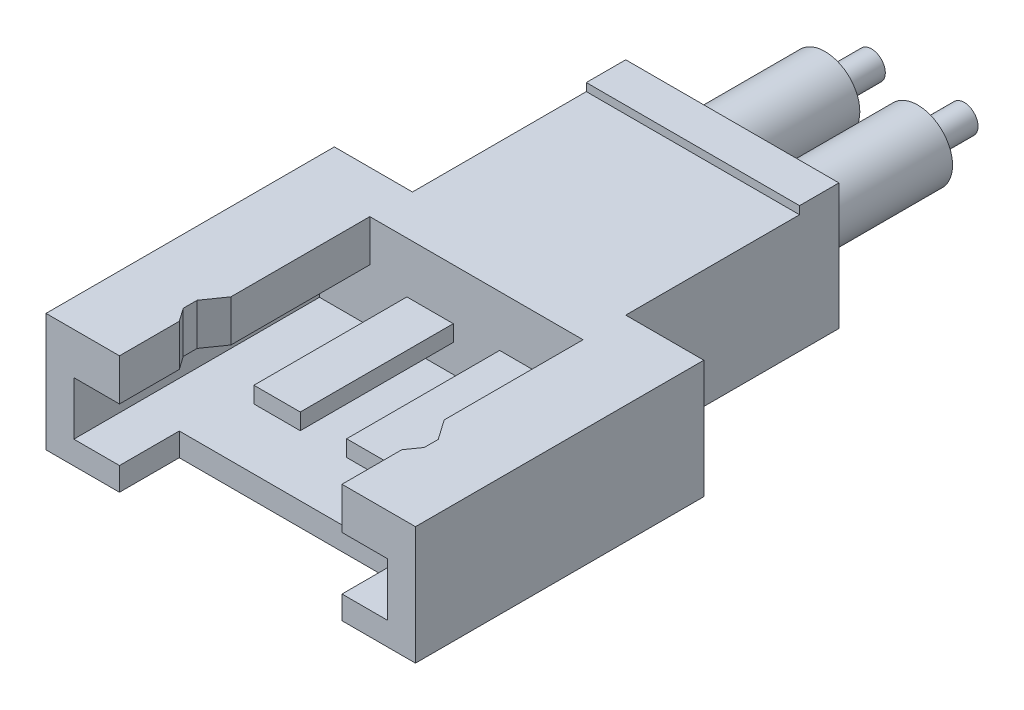
SolidWorks part; units mm, degrees
ref_plane "Front Plane" through (0, 0, 0) normal (0, 0, 1) x (1, 0, 0)
ref_plane "Top Plane" through (0, 0, 0) normal (0, 1, 0) x (1, 0, 0)
ref_plane "Right Plane" through (0, 0, 0) normal (1, 0, 0) x (0, 0, -1)
sketch "Sketch1" plane through (0, 0, 0) normal (0, 0, 1) x (1, 0, 0)
  line L1 (-2.3, 1.275) -> (2.3, 1.275)
  line L2 (-2.3, 1.275) -> (-2.3, -1.275)
  line L3 (-2.3, -1.275) -> (2.3, -1.275)
  line L4 (2.3, 1.275) -> (2.3, -1.275)
  line L5 (-2.3, 1.275) -> (2.3, -1.275) construction
  line L6 (-2.3, -1.275) -> (2.3, 1.275) construction
  point P0 (0, 0)
  dimension "D1" = 4.6
  dimension "D2" = 2.55
extrude "Boss-Extrude1" add sketch "Sketch1" along normal blind 4.6
sketch "Sketch2" plane through (0, 0, 4.6) normal (0, 0, 1) x (1, 0, 0)
  line L0 (2.3, 1.275) -> (-2.3, 1.275) construction
  line L1 (-3.985, 1.275) -> (3.985, 1.275)
  line L2 (-3.985, 1.275) -> (-3.985, -1.275)
  line L3 (-3.985, -1.275) -> (3.985, -1.275)
  line L4 (3.985, 1.275) -> (3.985, -1.275)
  line L5 (-3.985, 1.275) -> (3.985, -1.275) construction
  line L6 (-3.985, -1.275) -> (3.985, 1.275) construction
  point P0 (0, 0)
  dimension "D1" = 7.97
extrude "Boss-Extrude2" add sketch "Sketch2" along normal blind 6.22
sketch "Sketch3" plane through (0, 1.275, 0) normal (0, 1, 0) x (1, 0, 0)
  line L0 (2.3, -4.6) -> (2.3, 0) construction
  line L1 (-2.3, 0) -> (2.3, 0)
  line L2 (-2.3, 0) -> (-2.3, -0.85)
  line L3 (-2.3, -0.85) -> (2.3, -0.85)
  line L4 (2.3, 0) -> (2.3, -0.85)
  dimension "D1" = 0.85
extrude "Boss-Extrude3" add sketch "Sketch3" along normal offset from surface (0.17 mm away) 2.72 up to face at (0, -1.275, 5.005)
sketch "Sketch4" plane through (0, 0, 10.82) normal (0, 0, 1) x (1, 0, 0)
  line L0 (-3.985, -1.275) -> (3.985, -1.275) construction
  line L1 (-2.4, 1.275) -> (2.4, 1.275)
  line L2 (-2.4, 1.275) -> (-2.4, -1.275)
  line L3 (-2.4, -1.275) -> (2.4, -1.275)
  line L4 (2.4, 1.275) -> (2.4, -1.275)
  line L5 (-2.4, 1.275) -> (2.4, -1.275) construction
  line L6 (-2.4, -1.275) -> (2.4, 1.275) construction
  point P0 (0, 0)
  dimension "D1" = 4.8
extrude "Cut-Extrude1" cut sketch "Sketch4" against normal blind 1.29
sketch "Sketch5" plane through (0, 0, 10.82) normal (0, 0, 1) x (1, 0, 0)
  line L0 (0, 1.275) -> (0, -1.275) construction
  line L1 (-2.3, 1.275) -> (2.3, 1.275) construction
  line L2 (-2.4, -1.275) -> (2.4, -1.275) construction
  line L3 (-3.985, -1.275) -> (-2.4, -1.275) construction
  line L4 (-3.385, 0.375) -> (3.385, 0.375)
  line L5 (-3.385, 0.375) -> (-3.385, -0.775)
  line L6 (-3.385, -0.775) -> (3.385, -0.775)
  line L7 (3.385, 0.375) -> (3.385, -0.775)
  line L8 (-3.385, 0.375) -> (3.385, -0.775) construction
  line L9 (-3.385, -0.775) -> (3.385, 0.375) construction
  line L10 (-3.985, 1.275) -> (-3.985, -1.275) construction
  line L11 (-2.4, 1.275) -> (-3.985, 1.275) construction
  point P6 (0, -0.2)
  dimension "D1" = 0.5
  dimension "D2" = 0.6
  dimension "D3" = 0.9
extrude "Cut-Extrude2" cut sketch "Sketch5" against normal blind 5.3
sketch "Sketch6" plane through (0, 1.275, 0) normal (0, 1, 0) x (1, 0, 0)
  line L0 (0, -0.85) -> (0, -9.53) construction
  line L1 (-2.3, -0.85) -> (2.3, -0.85) construction
  line L2 (2.4, -9.53) -> (-2.4, -9.53) construction
  line L3 (-3.385, -5.52) -> (3.385, -5.52) construction
  line L4 (2.3, -5.52) -> (-2.3, -5.52)
  line L5 (2.3, -5.52) -> (2.3, -9.53)
  line L6 (2.3, -9.53) -> (-2.3, -9.53)
  line L7 (-2.3, -5.52) -> (-2.3, -9.53)
  line L8 (2.3, -5.52) -> (-2.3, -9.53) construction
  line L9 (2.3, -9.53) -> (-2.3, -5.52) construction
  line L10 (-2.4, -9.53) -> (-2.6, -9.2444)
  line L11 (-2.6, -9.2444) -> (-2.6, -8.9444)
  line L12 (-2.6, -8.9444) -> (-2.3, -8.5159)
  line L13 (-2.6, -9.0944) -> (-2.3, -9.0944) construction
  line L14 (-2.4, -9.53) -> (-2.3, -9.53)
  line L15 (2.6, -8.9444) -> (2.3, -8.5159)
  line L16 (2.6, -9.2444) -> (2.6, -8.9444)
  line L17 (2.4, -9.53) -> (2.6, -9.2444)
  line L18 (2.4, -9.53) -> (2.3, -9.53)
  point P6 (0, -7.525)
  line M3 (-2.4, -9.53) -> (2.4, -9.53)
  dimension "D1" = 4.6
  dimension "D2" = 0.3
  dimension "D3" = 145
  dimension "D4" = 0.3
extrude "Cut-Extrude3" cut sketch "Sketch6" against normal up to next contours L4 L7 L5 M3 | L12 L11 L10 L7 M3 | L17 L16 L15 L5 M3
sketch "Sketch7" plane through (0, 0, 5.52) normal (0, 0, 1) x (1, 0, 0)
  line L0 (-3.985, 0) -> (3.985, 0) construction
  line L1 (-3.985, 1.275) -> (-3.985, -1.275) construction
  line L2 (3.985, -1.275) -> (3.985, 1.275) construction
  line L3 (0, 1.445) -> (0, -1.275) construction
  line L4 (-2.3, 1.445) -> (2.3, 1.445) construction
  line L5 (-2.4, -1.275) -> (2.4, -1.275) construction
  line L6 (1.5, 0.175) -> (1.5, -0.175)
  line L7 (-1.5, 0.175) -> (-0.5, 0.175)
  line L8 (-1.5, 0.175) -> (-1.5, -0.175)
  line L9 (-1.5, -0.175) -> (-0.5, -0.175)
  line L10 (-0.5, 0.175) -> (-0.5, -0.175)
  line L11 (-1.5, 0.175) -> (-0.5, -0.175) construction
  line L12 (-1.5, -0.175) -> (-0.5, 0.175) construction
  line L13 (1.5, 0.175) -> (0.5, 0.175)
  line L14 (0.5, 0.175) -> (0.5, -0.175)
  line L15 (1.5, -0.175) -> (0.5, -0.175)
  point P12 (-1, 0)
  dimension "D1" = 0.35
  dimension "D2" = 1
  dimension "D3" = 2
extrude "Boss-Extrude4" add sketch "Sketch7" along normal offset from surface (3.3 mm away) 2 up to face at (-3.0425, -0.1, 10.82)
sketch "Sketch8" plane through (0, 0, 0) normal (0, 0, -1) x (-1, 0, 0)
  line L0 (-3.985, 0) -> (3.985, 0) construction
  line L1 (-3.985, -1.275) -> (-3.985, 1.275) construction
  line L2 (3.985, 1.275) -> (3.985, -1.275) construction
  line L3 (0, 1.445) -> (0, -1.275) construction
  line L4 (-2.3, 1.445) -> (2.3, 1.445) construction
  line L5 (2.3, -1.275) -> (-2.3, -1.275) construction
  circle A0 centre (-1, 0) radius 0.75
  circle A1 centre (1, 0) radius 0.75
  dimension "D2" = 1.5
  dimension "D1" = 2
extrude "Boss-Extrude5" add sketch "Sketch8" along normal blind 3
sketch "Sketch9" plane through (0, 0, -3) normal (0, 0, -1) x (-1, 0, 0)
  circle A0 centre (-1, 0) radius 0.3
  circle A1 centre (1, 0) radius 0.3
  dimension "D1" = 0.6
extrude "Boss-Extrude6" add sketch "Sketch9" along normal blind 1
